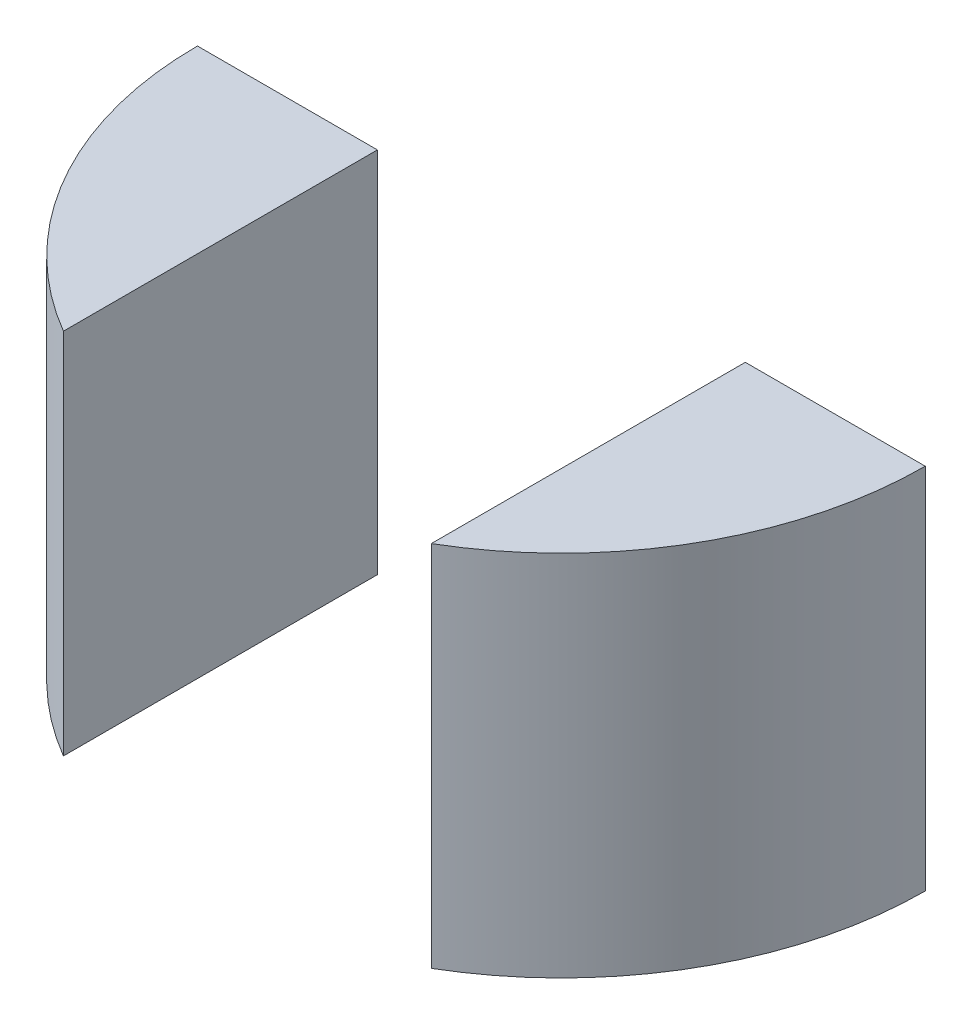
SolidWorks part; units mm, degrees
ref_plane "Front Plane" through (0, 0, 0) normal (0, 0, 1) x (1, 0, 0)
ref_plane "Top Plane" through (0, 0, 0) normal (0, 1, 0) x (1, 0, 0)
ref_plane "Right Plane" through (0, 0, 0) normal (1, 0, 0) x (0, 0, -1)
sketch "Sketch1" plane through (0, 0, 0) normal (0, 1, 0) x (1, 0, 0)
  circle A0 centre (0, 0) radius 5.025
  dimension "D1" = 10.05
extrude "Boss-Extrude1" add sketch "Sketch1" along normal blind 5.08
sketch "Sketch2" plane through (0, 5.08, 0) normal (0, 1, 0) x (1, 0, 0)
  line L1 (5.025, 0) -> (-272.9211, 0)
  line L2 (5.025, 0) -> (5.025, 253.0433)
  line L3 (5.025, 253.0433) -> (-272.9211, 253.0433)
  line L4 (-272.9211, 0) -> (-272.9211, 253.0433)
  circle A0 centre (0, 0) radius 5.025 construction
extrude "Cut-Extrude1" cut sketch "Sketch2" against normal blind 5.08
sketch "Sketch3" plane through (0, 0, 0) normal (0, 0, -1) x (-1, 0, 0)
  line L0 (-5.025, 0) -> (-2.54, 0) construction
  line L1 (5.025, 0) -> (-5.025, 0) construction
  line L2 (-2.54, 0) -> (2.54, 0) construction
  line L3 (2.54, 0) -> (5.025, 0) construction
  line L4 (5.025, 5.08) -> (-5.025, 5.08) construction
  line L5 (-2.54, 0) -> (2.54, 0)
  line L6 (-2.54, 0) -> (-2.54, 5.08)
  line L7 (-2.54, 5.08) -> (2.54, 5.08)
  line L8 (2.54, 0) -> (2.54, 5.08)
  dimension "D1" = 5.08
extrude "Cut-Extrude2" cut sketch "Sketch3" against normal blind 10
equation "\"MDFThickness\"= .2in"
equation "\"D1@Boss-Extrude1\"=\"MDFThickness\""
equation "\"D1@Sketch3\"=\"MDFThickness\""
equation "\"D1\" = 4.45mm"
